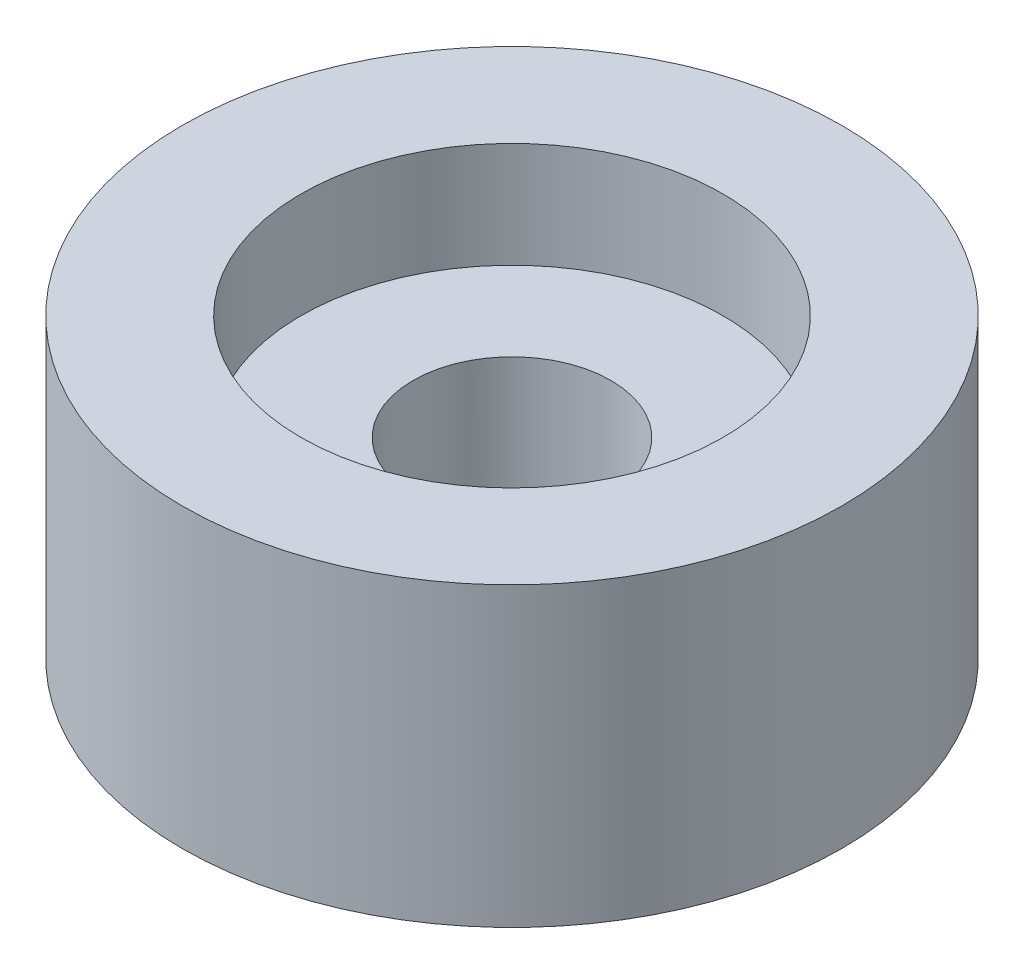
SolidWorks part; units mm, degrees
material "ABS"
ref_plane "Front Plane" through (0, 0, 0) normal (0, 0, 1) x (1, 0, 0)
ref_plane "Top Plane" through (0, 0, 0) normal (0, 1, 0) x (1, 0, 0)
ref_plane "Right Plane" through (0, 0, 0) normal (1, 0, 0) x (0, 0, -1)
sketch "Sketch1" plane through (0, 0, 0) normal (0, 0, 1) x (1, 0, 0)
  line L0 (0, 0) -> (0, 9) construction
  line L1 (0, 9) -> (3, 9) construction
  line L2 (3, 9) -> (3, 0)
  line L5 (3, 0) -> (0, 0) construction
  line L6 (3, 0) -> (10, 0)
  line L7 (10, 0) -> (10, 9)
  line L8 (10, 9) -> (3, 9)
  dimension "D2" = 6
  dimension "D4" = 9
  dimension "D5" = 20
revolve "Revolve1" add sketch "Sketch1" angle 360 about L0
sketch "Sketch2" plane through (0, 9, 0) normal (0, 1, 0) x (1, 0, 0)
  circle A0 centre (0, 0) radius 6.4
  dimension "D1" = 12.8
extrude "Cut-Extrude1" cut sketch "Sketch2" against normal blind 3.2
